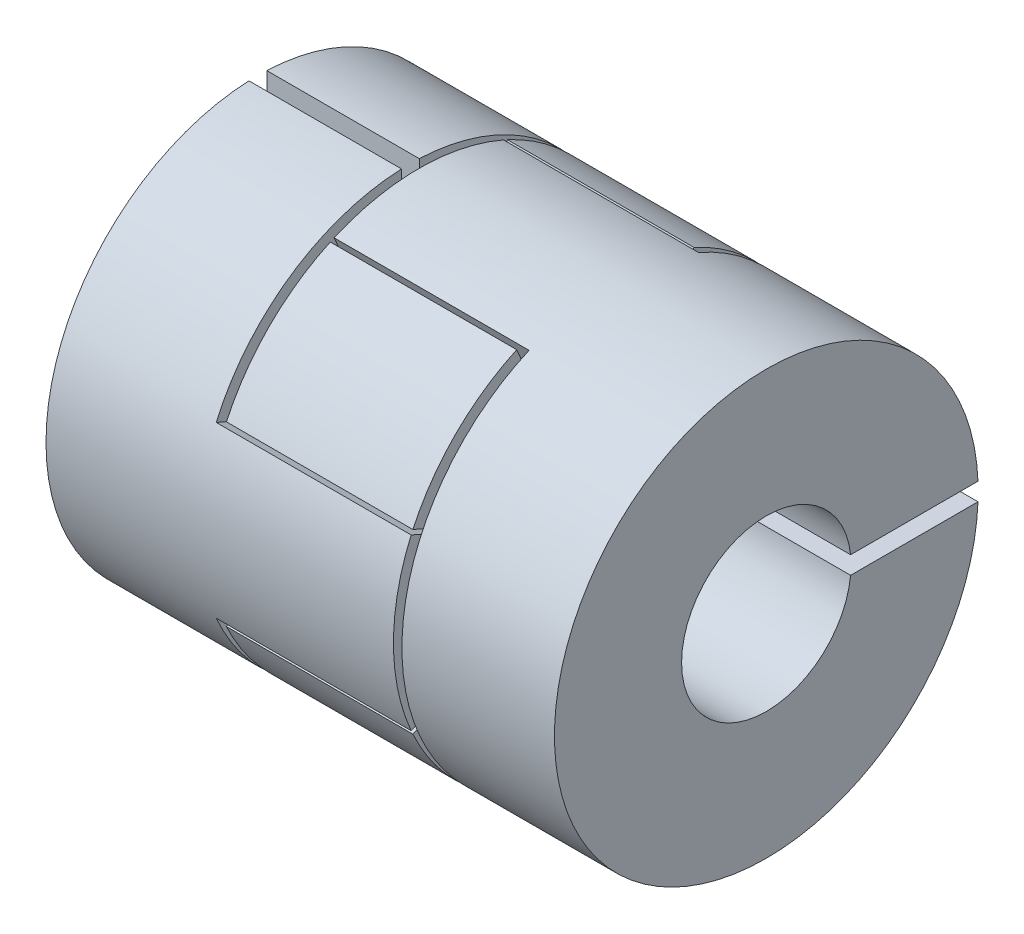
SolidWorks part; units mm, degrees
ref_plane "Front Plane" through (0, 0, 0) normal (0, 0, 1) x (1, 0, 0)
ref_plane "Top Plane" through (0, 0, 0) normal (0, 1, 0) x (1, 0, 0)
ref_plane "Right Plane" through (0, 0, 0) normal (1, 0, 0) x (0, 0, -1)
ref_plane "Plane1" through (15, 0, 0) normal (1, 0, 0) x (0, 0, -1)
sketch "Sketch1" plane through (15, 0, 0) normal (1, 0, 0) x (0, 0, -1)
  circle A0 centre (0, 0) radius 12.5
  circle A2 centre (0, 0) radius 5
  dimension "D1" = 25
  dimension "D2" = 10
extrude "Boss-Extrude1" add sketch "Sketch1" against normal blind 9
sketch "Sketch3" plane through (6, 0, 0) normal (-1, 0, 0) x (0, 0, 1)
  line L0 (2.4, 5.4991) -> (5, 11.4564)
  line L1 (5, 11.4564) -> (-5, 11.4564) construction
  line L2 (-5, 11.4564) -> (-2.4, 5.4991)
  line L3 (-2, 4.5826) -> (0, 0) construction
  line L4 (0, 0) -> (2, 4.5826) construction
  line L5 (0, 0) -> (12.5, 0) construction
  line L6 (2.4, -5.4991) -> (5, -11.4564)
  line L7 (-5, -11.4564) -> (-2.4, -5.4991)
  line L8 (-2.4, -5.4991) -> (-2, -4.5826) construction
  line L9 (2, -4.5826) -> (2.4, -5.4991) construction
  line L10 (-2.4, 5.4991) -> (-2, 4.5826) construction
  line L11 (2, 4.5826) -> (2.4, 5.4991) construction
  circle A0 centre (0, 0) radius 5 construction
  circle A1 centre (0, 0) radius 12.5 construction
  arc A2 (5, 11.4564) -> (-5, 11.4564) centre (0, 0) ccw
  arc A3 (2, 4.5826) -> (-2, 4.5826) centre (0, 0) ccw construction
  arc A4 (5, -11.4564) -> (-5, -11.4564) centre (0, 0) cw
  arc A5 (2, -4.5826) -> (-2, -4.5826) centre (0, 0) cw construction
  arc A6 (-2.4, -5.4991) -> (2.4, -5.4991) centre (0, 0) ccw
  arc A7 (-2.4, 5.4991) -> (-2.4, -5.4991) centre (0, 0) ccw construction
  arc A8 (2.4, -5.4991) -> (6, 0) centre (0, 0) ccw construction
  arc A9 (2.4, 5.4991) -> (-2.4, 5.4991) centre (0, 0) ccw
  arc A10 (6, 0) -> (2.4, 5.4991) centre (0, 0) ccw construction
  dimension "D2" = 12
  dimension "D1" = 10
extrude "Boss-Extrude3" add sketch "Sketch3" along normal blind 11.5
sketch "Sketch4" plane through (15, 0, 0) normal (1, 0, 0) x (0, 0, -1)
  line L0 (0, 0) -> (5, 0) construction
  line L1 (5, 0) -> (12.5, 0) construction
  line L2 (4.9724, -0.525) -> (12.489, -0.525)
  line L3 (4.9724, 0.525) -> (12.489, 0.525)
  line L4 (5, 0.525) -> (12.5, 0.525) construction
  line L5 (5, -0.525) -> (12.5, -0.525) construction
  circle A0 centre (0, 0) radius 5 construction
  circle A1 centre (0, 0) radius 12.5 construction
  arc A2 (12.489, -0.525) -> (12.489, 0.525) centre (0, 0) ccw
  arc A3 (4.9724, -0.525) -> (4.9724, 0.525) centre (0, 0) ccw
  dimension "D1" = 0.525
  dimension "D2" = 0.525
extrude "Cut-Extrude1" cut sketch "Sketch4" against normal through all
ref_plane "Plane2" through (-15, 0, 0) normal (1, 0, 0) x (0, 0, -1)
sketch "Sketch5" plane through (-15, 0, 0) normal (1, 0, 0) x (0, 0, -1)
  arc A0 (12.489, 0.525) -> (12.489, -0.525) centre (0, 0) ccw construction
  arc A1 (12.489, 0.525) -> (12.489, -0.525) centre (0, 0) ccw construction
  circle A2 centre (0, 0) radius 3.175
  circle A3 centre (0, 0) radius 12.5
  dimension "D1" = 6.35
extrude "Boss-Extrude5" add sketch "Sketch5" along normal blind 9 separate body
sketch "Sketch6" plane through (-15, 0, 0) normal (-1, 0, 0) x (0, 0, 1)
  line L0 (0, 0) -> (0, 3.175) construction
  line L1 (0, 3.175) -> (0, 12.5) construction
  line L2 (0.525, 3.1313) -> (0.525, 12.489)
  line L3 (-0.525, 3.1313) -> (-0.525, 12.489)
  line L4 (-0.525, 3.175) -> (-0.525, 12.5) construction
  line L5 (0.525, 3.175) -> (0.525, 12.5) construction
  circle A0 centre (0, 0) radius 3.175 construction
  circle A1 centre (0, 0) radius 12.5 construction
  arc A2 (0.525, 3.1313) -> (-0.525, 3.1313) centre (0, 0) ccw
  circle A3 centre (0, 0) radius 12.5
  arc A4 (0.525, 12.489) -> (-0.525, 12.489) centre (0, 0) ccw
  dimension "D1" = 0.525
  dimension "D2" = 0.525
  dimension "D3" = 0
extrude "Cut-Extrude2" cut sketch "Sketch6" against normal up to next (9 mm away)
sketch "Sketch7" plane through (-6, 0, 0) normal (1, 0, 0) x (0, 0, -1)
  line L0 (5.4991, 2.4) -> (11.4564, 5)
  line L1 (11.4564, 5) -> (11.4564, -5) construction
  line L2 (11.4564, -5) -> (5.4991, -2.4)
  line L3 (2.9099, -1.27) -> (0, 0) construction
  line L4 (0, 0) -> (2.9099, 1.27) construction
  line L5 (0, 0) -> (0, -12.5) construction
  line L6 (-5.4991, 2.4) -> (-11.4564, 5)
  line L7 (-11.4564, -5) -> (-5.4991, -2.4)
  line L8 (2.9099, 1.27) -> (5.4991, 2.4) construction
  line L9 (5.4991, -2.4) -> (2.9099, -1.27) construction
  line L10 (-5.4991, -2.4) -> (-2.9099, -1.27) construction
  line L11 (-2.9099, 1.27) -> (-5.4991, 2.4) construction
  arc A2 (-0.525, 12.489) -> (0.525, 12.489) centre (0, 0) ccw construction
  arc A3 (11.4564, -5) -> (11.4564, 5) centre (0, 0) ccw
  arc A4 (-11.4564, -5) -> (-11.4564, 5) centre (0, 0) cw
  arc A6 (-5.4991, 2.4) -> (-5.4991, -2.4) centre (0, 0) ccw
  arc A7 (5.4991, 2.4) -> (-5.4991, 2.4) centre (0, 0) ccw construction
  arc A8 (0, -6) -> (5.4991, -2.4) centre (0, 0) ccw construction
  arc A9 (5.4991, -2.4) -> (5.4991, 2.4) centre (0, 0) ccw
  arc A10 (-5.4991, -2.4) -> (0, -6) centre (0, 0) ccw construction
  dimension "D2" = 12
  dimension "D1" = 10
extrude "Boss-Extrude6" add sketch "Sketch7" along normal blind 11.5
sketch "Sketch8" plane through (-5.5, 0, 0) normal (-1, 0, 0) x (0, 0, 1)
  line L0 (5.3281, -11.5833) -> (5.2281, -11.3541) construction
  line L1 (5.3281, -11.5833) -> (2.527, -5.165) construction
  line L2 (-2.4, -5.4991) -> (-5, -11.4564) construction
  line L3 (5, -11.4564) -> (2.4, -5.4991) construction
  line L6 (11.3541, 5.2281) -> (11.5833, 5.3281) construction
  line L7 (5.165, 2.527) -> (11.5833, 5.3281) construction
  line L8 (11.5833, -5.3281) -> (11.3541, -5.2281) construction
  line L9 (11.5833, -5.3281) -> (5.165, -2.527) construction
  line L24 (-5.4991, -2.4) -> (-11.4564, -5) construction
  line L25 (-11.4564, 5) -> (-5.4991, 2.4) construction
  line L26 (-5, 11.4564) -> (-2.4, 5.4991) construction
  line L27 (2.4, 5.4991) -> (5, 11.4564) construction
  line L28 (11.4564, -5) -> (5.4991, -2.4) construction
  line L29 (5.4991, 2.4) -> (11.4564, 5) construction
  line L30 (-2.4, -5.4991) -> (-5, -11.4564) construction
  line L31 (5, -11.4564) -> (2.4, -5.4991) construction
  line L32 (-5.4991, -2.4) -> (-11.4564, -5) construction
  line L33 (-11.4564, 5) -> (-5.4991, 2.4) construction
  line L34 (-5, 11.4564) -> (-2.4, 5.4991) construction
  line L35 (2.4, 5.4991) -> (5, 11.4564) construction
  line L36 (11.4564, -5) -> (5.4991, -2.4) construction
  line L37 (5.4991, 2.4) -> (11.4564, 5) construction
  line L38 (5.2281, -11.3541) -> (2.527, -5.165)
  line L39 (-2.527, -5.165) -> (-5.2281, -11.3541)
  line L40 (-5.165, -2.527) -> (-11.3541, -5.2281)
  line L41 (-11.3541, 5.2281) -> (-5.165, 2.527)
  line L42 (-5.2281, 11.3541) -> (-2.527, 5.165)
  line L43 (2.527, 5.165) -> (5.2281, 11.3541)
  line L44 (5.165, 2.527) -> (11.3541, 5.2281)
  line L45 (11.3541, -5.2281) -> (5.165, -2.527)
  line L46 (5.2281, 11.3541) -> (5.3281, 11.5833) construction
  line L47 (2.527, 5.165) -> (5.3281, 11.5833) construction
  line L48 (-5.3281, 11.5833) -> (-5.2281, 11.3541) construction
  line L49 (-5.3281, 11.5833) -> (-2.527, 5.165) construction
  line L50 (-11.5833, 5.3281) -> (-11.3541, 5.2281) construction
  line L51 (-11.5833, 5.3281) -> (-5.165, 2.527) construction
  line L52 (-11.3541, -5.2281) -> (-11.5833, -5.3281) construction
  line L53 (-5.165, -2.527) -> (-11.5833, -5.3281) construction
  line L54 (-5.2281, -11.3541) -> (-5.3281, -11.5833) construction
  line L55 (-2.527, -5.165) -> (-5.3281, -11.5833) construction
  arc A0 (5, -11.4564) -> (5.2281, -11.3541) centre (0, 0) ccw construction
  arc A1 (11.4564, -5) -> (11.4564, 5) centre (0, 0) ccw construction
  arc A2 (-2.4, -5.4991) -> (2.4, -5.4991) centre (0, 0) ccw construction
  arc A3 (-5, -11.4564) -> (5, -11.4564) centre (0, 0) ccw construction
  arc A6 (11.3541, 5.2281) -> (5.2281, 11.3541) centre (0, 0) ccw
  arc A7 (11.4564, 5) -> (11.3541, 5.2281) centre (0, 0) ccw construction
  arc A8 (11.3541, -5.2281) -> (11.4564, -5) centre (0, 0) ccw construction
  arc A25 (-5.4991, 2.4) -> (-5.4991, -2.4) centre (0, 0) ccw construction
  arc A26 (-11.4564, 5) -> (-11.4564, -5) centre (0, 0) ccw construction
  arc A27 (5, 11.4564) -> (-5, 11.4564) centre (0, 0) ccw construction
  arc A28 (2.4, 5.4991) -> (-2.4, 5.4991) centre (0, 0) ccw construction
  arc A30 (11.4564, -5) -> (11.4564, 5) centre (0, 0) ccw construction
  arc A31 (5.4991, -2.4) -> (5.4991, 2.4) centre (0, 0) ccw construction
  arc A32 (-2.4, -5.4991) -> (2.4, -5.4991) centre (0, 0) ccw construction
  arc A34 (-5, -11.4564) -> (5, -11.4564) centre (0, 0) ccw construction
  arc A35 (-5.4991, 2.4) -> (-5.4991, -2.4) centre (0, 0) ccw construction
  arc A36 (-11.4564, 5) -> (-11.4564, -5) centre (0, 0) ccw construction
  arc A38 (5, 11.4564) -> (-5, 11.4564) centre (0, 0) ccw construction
  arc A39 (2.4, 5.4991) -> (-2.4, 5.4991) centre (0, 0) ccw construction
  arc A40 (11.4564, -5) -> (11.4564, 5) centre (0, 0) ccw construction
  arc A41 (5.4991, -2.4) -> (5.4991, 2.4) centre (0, 0) ccw construction
  arc A42 (-2.527, -5.165) -> (2.527, -5.165) centre (0, 0) ccw
  arc A43 (-5.3281, -11.5833) -> (5.3281, -11.5833) centre (0, 0) ccw construction
  arc A44 (-5.165, 2.527) -> (-5.165, -2.527) centre (0, 0) ccw
  arc A45 (-11.5833, 5.3281) -> (-11.5833, -5.3281) centre (0, 0) ccw construction
  arc A46 (5.3281, 11.5833) -> (-5.3281, 11.5833) centre (0, 0) ccw construction
  arc A47 (2.527, 5.165) -> (-2.527, 5.165) centre (0, 0) ccw
  arc A48 (11.5833, -5.3281) -> (11.5833, 5.3281) centre (0, 0) ccw construction
  arc A49 (5.165, -2.527) -> (5.165, 2.527) centre (0, 0) ccw
  arc A50 (-5.2281, 11.3541) -> (-11.3541, 5.2281) centre (0, 0) ccw
  arc A51 (5.2281, 11.3541) -> (5, 11.4564) centre (0, 0) ccw construction
  arc A52 (5, 11.4564) -> (-5, 11.4564) centre (0, 0) ccw construction
  arc A53 (-5, 11.4564) -> (-5.2281, 11.3541) centre (0, 0) ccw construction
  arc A54 (-11.3541, 5.2281) -> (-11.4564, 5) centre (0, 0) ccw construction
  arc A55 (-11.3541, -5.2281) -> (-5.2281, -11.3541) centre (0, 0) ccw
  arc A56 (-11.4564, 5) -> (-11.4564, -5) centre (0, 0) ccw construction
  arc A57 (-11.4564, -5) -> (-11.3541, -5.2281) centre (0, 0) ccw construction
  arc A58 (-5, -11.4564) -> (5, -11.4564) centre (0, 0) ccw construction
  arc A59 (5.2281, -11.3541) -> (11.3541, -5.2281) centre (0, 0) ccw
  arc A60 (-5.2281, -11.3541) -> (-5, -11.4564) centre (0, 0) ccw construction
  dimension "D1" = 0.25
extrude "Boss-Extrude7" add sketch "Sketch8" against normal up to surface (11 mm away) separate body up to face at (5.5, 0, -8.8639)
